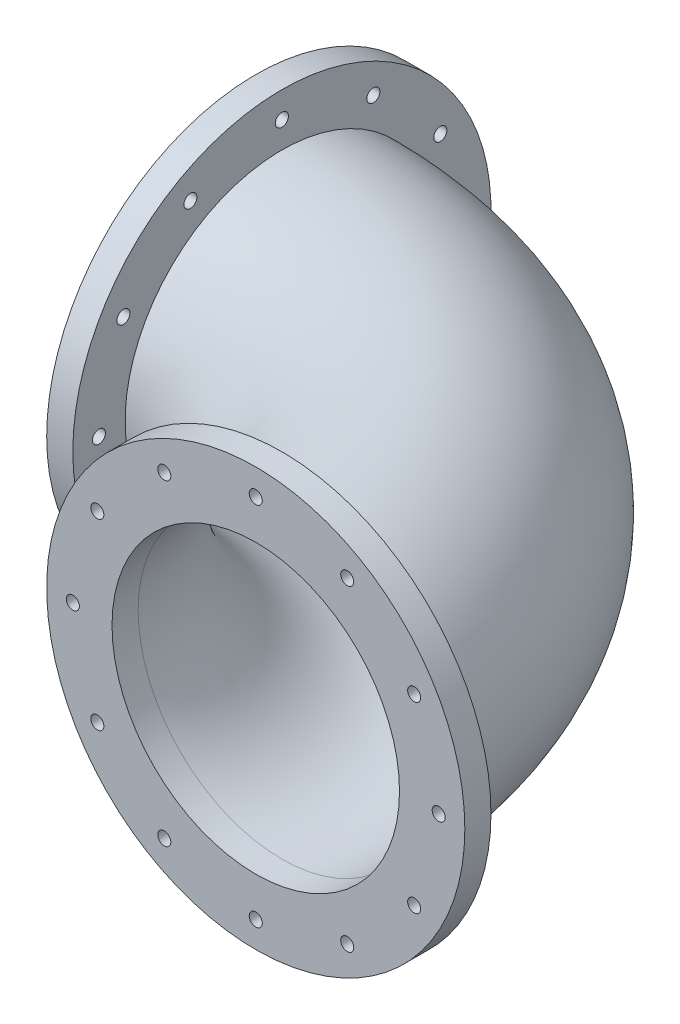
SolidWorks part; units mm, degrees
material "Plain Carbon Steel"
ref_plane "Front Plane" through (0, 0, 0) normal (0, 0, 1) x (1, 0, 0)
ref_plane "Top Plane" through (0, 0, 0) normal (0, 1, 0) x (1, 0, 0)
ref_plane "Right Plane" through (0, 0, 0) normal (1, 0, 0) x (0, 0, -1)
sketch "Sketch1" plane through (0, 0, 0) normal (0, 1, 0) x (1, 0, 0)
  arc A0 (0, 152.4) -> (152.4, 0) centre (0, 0) cw
  dimension "D1" = 152.4
sketch "Sketch2" plane through (0, 0, 0) normal (1, 0, 0) x (0, 0, -1)
  circle A0 centre (152.4, 0) radius 69.85
  circle A1 centre (152.4, 0) radius 76.2
  dimension "D1" = 139.7
  dimension "D2" = 152.4
sweep "Sweep1" add profiles "Sketch2" path "Sketch1"
ref_plane "Plane1" through (0, 0, 0) normal (-1, 0, 0) x (0, 0, 1)
sketch "Sketch3" plane through (0, 0, 0) normal (-1, 0, 0) x (0, 0, 1)
  line L0 (-254, 0) -> (-50.8, 0) construction
  line L1 (-152.4, -101.6) -> (-152.4, 101.6) construction
  line L2 (-152.4, 0) -> (-241.3, 0) construction
  line L3 (-152.4, 0) -> (-229.3897, -44.45) construction
  line L4 (0, -69.85) -> (0, 69.85) construction
  circle A0 centre (-152.4, 0) radius 76.2 construction
  circle A1 centre (-152.4, 0) radius 69.85 construction
  circle A2 centre (-152.4, 0) radius 76.2 construction
  circle A3 centre (-152.4, 0) radius 69.85
  circle A4 centre (-152.4, 0) radius 101.6
  circle A5 centre (-152.4, 0) radius 88.9 construction
  circle A6 centre (-241.3, 0) radius 3.175
  circle A7 centre (-229.3897, -44.45) radius 3.175
  circle A8 centre (-196.85, -76.9897) radius 3.175
  circle A9 centre (-152.4, -88.9) radius 3.175
  circle A10 centre (-107.95, -76.9897) radius 3.175
  circle A11 centre (-75.4103, -44.45) radius 3.175
  circle A12 centre (-63.5, 0) radius 3.175
  circle A13 centre (-75.4103, 44.45) radius 3.175
  circle A14 centre (-107.95, 76.9897) radius 3.175
  circle A15 centre (-152.4, 88.9) radius 3.175
  circle A16 centre (-196.85, 76.9897) radius 3.175
  circle A17 centre (-229.3897, 44.45) radius 3.175
  dimension "D1" = 203.2
  dimension "D2" = 177.8
  dimension "D3" = 6.35
  dimension "D5" = 30
  dimension "D6" = 88.9
  dimension "D4" = 12
extrude "Boss-Extrude1" add sketch "Sketch3" along normal blind 12.7 contours A4 | A3 | A8 | A9 | A10 | A11 | A12 | A13 | A14 | A15 | A16 | A17 | A6 | A7
ref_plane "Plane2" through (0, 0, 0) normal (0, 0, 1) x (1, 0, 0)
sketch "Sketch5" plane through (0, 0, 0) normal (0, 0, 1) x (1, 0, 0)
  line L1 (152.4, 101.6) -> (152.4, -101.6) construction
  line L2 (50.8, 0) -> (254, 0) construction
  circle A0 centre (152.4, 0) radius 76.2 construction
  circle A1 centre (152.4, 0) radius 69.85 construction
  circle A2 centre (152.4, 0) radius 76.2 construction
  circle A3 centre (152.4, 0) radius 69.85
  circle A4 centre (152.4, 0) radius 101.6
  circle A5 centre (152.4, 0) radius 88.9 construction
  circle A6 centre (152.4, 88.9) radius 3.175
  circle A7 centre (196.85, 76.9897) radius 3.175
  circle A8 centre (229.3897, 44.45) radius 3.175
  circle A9 centre (241.3, 0) radius 3.175
  circle A10 centre (229.3897, -44.45) radius 3.175
  circle A11 centre (196.85, -76.9897) radius 3.175
  circle A12 centre (152.4, -88.9) radius 3.175
  circle A13 centre (107.95, -76.9897) radius 3.175
  circle A14 centre (75.4103, -44.45) radius 3.175
  circle A15 centre (63.5, 0) radius 3.175
  circle A16 centre (75.4103, 44.45) radius 3.175
  circle A17 centre (107.95, 76.9897) radius 3.175
  point P38 (152.4, 0)
  dimension "D1" = 203.2
  dimension "D2" = 177.8
  dimension "D3" = 6.35
  dimension "D4" = 12
extrude "Boss-Extrude2" add sketch "Sketch5" along normal blind 12.7 contours A4 | A3 | A8 | A7 | A6 | A17 | A16 | A15 | A14 | A13 | A11 | A12 | A10 | A9
